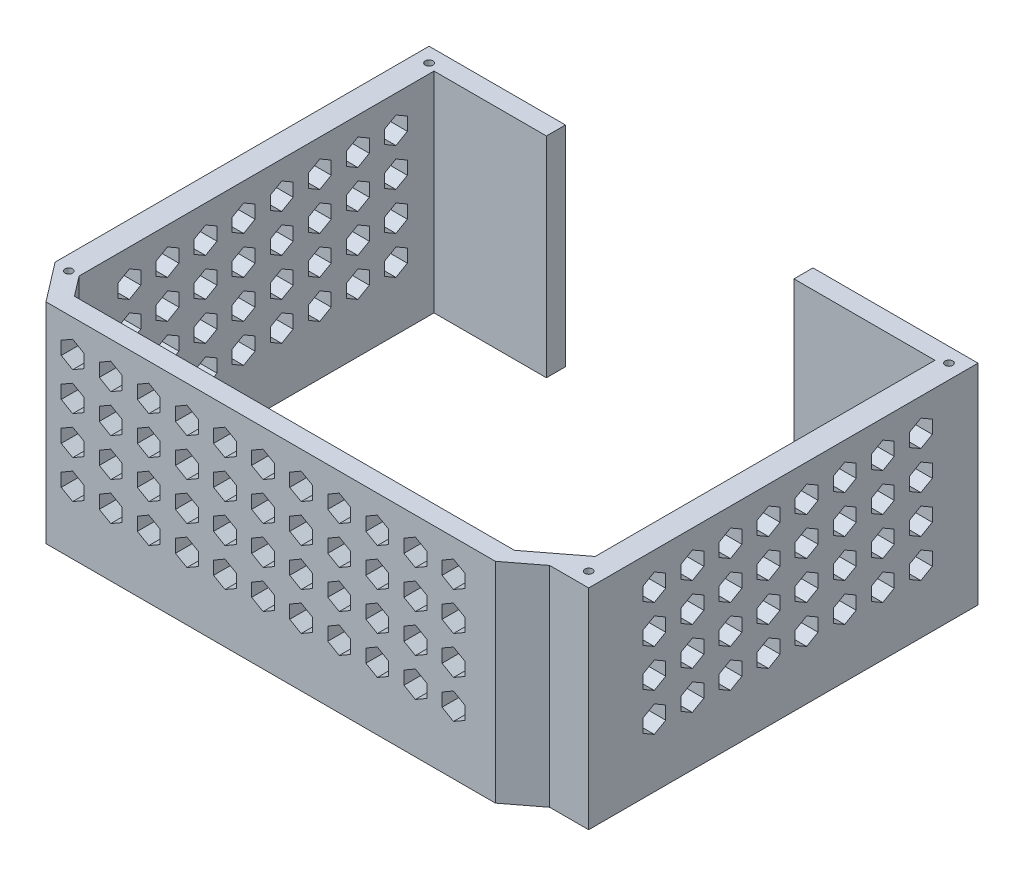
SolidWorks part; units mm, degrees
ref_plane "Front Plane" through (0, 0, 0) normal (0, 0, 1) x (1, 0, 0)
ref_plane "Top Plane" through (0, 0, 0) normal (0, 1, 0) x (1, 0, 0)
ref_plane "Right Plane" through (0, 0, 0) normal (1, 0, 0) x (0, 0, -1)
sketch "Sketch1" plane through (0, 0, 0) normal (0, 1, 0) x (1, 0, 0)
  line L0 (68.26, 0) -> (68.26, 47.305) construction
  line L1 (68.26, 47.305) -> (0, 47.305) construction
  line L2 (-3.815, 98.425) -> (-3.815, 0.2182)
  line L4 (-3.815, 0.2182) -> (4.0178, -10)
  line L5 (4.0178, -10) -> (122.03, -10)
  line L6 (122.03, -10) -> (130.0986, -3.815)
  line L7 (130.0986, -3.815) -> (140.33, -3.815)
  line L8 (140.33, -3.815) -> (140.33, 98.425)
  line L9 (140.33, 98.425) -> (97, 98.425)
  line L10 (97, 98.425) -> (97, 93.425)
  line L11 (97, 93.425) -> (134.03, 93.425)
  line L12 (134.03, 93.425) -> (134.03, 4.1986)
  line L13 (134.03, 4.1986) -> (122.03, -5)
  line L14 (122.03, -5) -> (6.485, -5)
  line L15 (6.485, -5) -> (2.485, 0.2182)
  line L16 (2.485, 0.2182) -> (2.485, 93.425)
  line L17 (2.485, 93.425) -> (32, 93.425)
  line L18 (32, 93.425) -> (32, 98.425)
  line L19 (32, 98.425) -> (-3.815, 98.425)
  circle A0 centre (0, 0) radius 1
  circle A1 centre (136.52, 0) radius 1
  circle A2 centre (136.52, 94.61) radius 1
  circle A3 centre (0, 94.61) radius 1
  dimension "D1" = 2
  dimension "D2" = 136.52
  dimension "D3" = 94.61
  dimension "D4" = 144.145
  dimension "D5" = 3.815
  dimension "D6" = 6.3
  dimension "D7" = 3.815
  dimension "D8" = 5
  dimension "D9" = 5
  dimension "D10" = 5
  dimension "D11" = 4
  dimension "D12" = 65
  dimension "D13" = 32
  dimension "D14" = 5
  dimension "D15" = 6.3
  dimension "D16" = 12
  dimension "D17" = 3.815
extrude "Boss-Extrude1" add sketch "Sketch1" along normal blind 55
sketch "Sketch2" plane through (0, 0, 10) normal (0, 0, 1) x (1, 0, 0)
  line L0 (4.0178, 55) -> (4.0178, 0) construction
  line L1 (11.0178, 43.0718) -> (14.0178, 44.8038)
  line L2 (14.0178, 44.8038) -> (14.0178, 48.2679)
  line L3 (14.0178, 48.2679) -> (11.0178, 50)
  line L4 (11.0178, 50) -> (8.0178, 48.2679)
  line L5 (8.0178, 48.2679) -> (8.0178, 44.8038)
  line L6 (8.0178, 44.8038) -> (11.0178, 43.0718)
  line L7 (4.0178, 55) -> (122.03, 55) construction
  line L8 (21.0178, 43.0718) -> (24.0178, 44.8038)
  line L9 (24.0178, 44.8038) -> (24.0178, 48.2679)
  line L10 (24.0178, 48.2679) -> (21.0178, 50)
  line L11 (21.0178, 50) -> (18.0178, 48.2679)
  line L12 (18.0178, 48.2679) -> (18.0178, 44.8038)
  line L13 (18.0178, 44.8038) -> (21.0178, 43.0718)
  line L14 (31.0178, 43.0718) -> (34.0178, 44.8038)
  line L15 (34.0178, 44.8038) -> (34.0178, 48.2679)
  line L16 (34.0178, 48.2679) -> (31.0178, 50)
  line L17 (31.0178, 50) -> (28.0178, 48.2679)
  line L18 (28.0178, 48.2679) -> (28.0178, 44.8038)
  line L19 (28.0178, 44.8038) -> (31.0178, 43.0718)
  line L20 (41.0178, 43.0718) -> (44.0178, 44.8038)
  line L21 (44.0178, 44.8038) -> (44.0178, 48.2679)
  line L22 (44.0178, 48.2679) -> (41.0178, 50)
  line L23 (41.0178, 50) -> (38.0178, 48.2679)
  line L24 (38.0178, 48.2679) -> (38.0178, 44.8038)
  line L25 (38.0178, 44.8038) -> (41.0178, 43.0718)
  line L26 (51.0178, 43.0718) -> (54.0178, 44.8038)
  line L27 (54.0178, 44.8038) -> (54.0178, 48.2679)
  line L28 (54.0178, 48.2679) -> (51.0178, 50)
  line L29 (51.0178, 50) -> (48.0178, 48.2679)
  line L30 (48.0178, 48.2679) -> (48.0178, 44.8038)
  line L31 (48.0178, 44.8038) -> (51.0178, 43.0718)
  line L32 (61.0178, 43.0718) -> (64.0178, 44.8038)
  line L33 (64.0178, 44.8038) -> (64.0178, 48.2679)
  line L34 (64.0178, 48.2679) -> (61.0178, 50)
  line L35 (61.0178, 50) -> (58.0178, 48.2679)
  line L36 (58.0178, 48.2679) -> (58.0178, 44.8038)
  line L37 (58.0178, 44.8038) -> (61.0178, 43.0718)
  line L38 (71.0178, 43.0718) -> (74.0178, 44.8038)
  line L39 (74.0178, 44.8038) -> (74.0178, 48.2679)
  line L40 (74.0178, 48.2679) -> (71.0178, 50)
  line L41 (71.0178, 50) -> (68.0178, 48.2679)
  line L42 (68.0178, 48.2679) -> (68.0178, 44.8038)
  line L43 (68.0178, 44.8038) -> (71.0178, 43.0718)
  line L44 (81.0178, 43.0718) -> (84.0178, 44.8038)
  line L45 (84.0178, 44.8038) -> (84.0178, 48.2679)
  line L46 (84.0178, 48.2679) -> (81.0178, 50)
  line L47 (81.0178, 50) -> (78.0178, 48.2679)
  line L48 (78.0178, 48.2679) -> (78.0178, 44.8038)
  line L49 (78.0178, 44.8038) -> (81.0178, 43.0718)
  line L50 (91.0178, 43.0718) -> (94.0178, 44.8038)
  line L51 (94.0178, 44.8038) -> (94.0178, 48.2679)
  line L52 (94.0178, 48.2679) -> (91.0178, 50)
  line L53 (91.0178, 50) -> (88.0178, 48.2679)
  line L54 (88.0178, 48.2679) -> (88.0178, 44.8038)
  line L55 (88.0178, 44.8038) -> (91.0178, 43.0718)
  line L56 (101.0178, 43.0718) -> (104.0178, 44.8038)
  line L57 (104.0178, 44.8038) -> (104.0178, 48.2679)
  line L58 (104.0178, 48.2679) -> (101.0178, 50)
  line L59 (101.0178, 50) -> (98.0178, 48.2679)
  line L60 (98.0178, 48.2679) -> (98.0178, 44.8038)
  line L61 (98.0178, 44.8038) -> (101.0178, 43.0718)
  line L62 (111.0178, 43.0718) -> (114.0178, 44.8038)
  line L63 (114.0178, 44.8038) -> (114.0178, 48.2679)
  line L64 (114.0178, 48.2679) -> (111.0178, 50)
  line L65 (111.0178, 50) -> (108.0178, 48.2679)
  line L66 (108.0178, 48.2679) -> (108.0178, 44.8038)
  line L67 (108.0178, 44.8038) -> (111.0178, 43.0718)
  line L68 (21.0178, 33.0718) -> (24.0178, 34.8038)
  line L69 (24.0178, 34.8038) -> (24.0178, 38.2679)
  line L70 (24.0178, 38.2679) -> (21.0178, 40)
  line L71 (21.0178, 40) -> (18.0178, 38.2679)
  line L72 (18.0178, 38.2679) -> (18.0178, 34.8038)
  line L73 (18.0178, 34.8038) -> (21.0178, 33.0718)
  line L74 (31.0178, 33.0718) -> (34.0178, 34.8038)
  line L75 (34.0178, 34.8038) -> (34.0178, 38.2679)
  line L76 (34.0178, 38.2679) -> (31.0178, 40)
  line L77 (31.0178, 40) -> (28.0178, 38.2679)
  line L78 (28.0178, 38.2679) -> (28.0178, 34.8038)
  line L79 (28.0178, 34.8038) -> (31.0178, 33.0718)
  line L80 (41.0178, 33.0718) -> (44.0178, 34.8038)
  line L81 (44.0178, 34.8038) -> (44.0178, 38.2679)
  line L82 (44.0178, 38.2679) -> (41.0178, 40)
  line L83 (41.0178, 40) -> (38.0178, 38.2679)
  line L84 (38.0178, 38.2679) -> (38.0178, 34.8038)
  line L85 (38.0178, 34.8038) -> (41.0178, 33.0718)
  line L86 (51.0178, 33.0718) -> (54.0178, 34.8038)
  line L87 (54.0178, 34.8038) -> (54.0178, 38.2679)
  line L88 (54.0178, 38.2679) -> (51.0178, 40)
  line L89 (51.0178, 40) -> (48.0178, 38.2679)
  line L90 (48.0178, 38.2679) -> (48.0178, 34.8038)
  line L91 (48.0178, 34.8038) -> (51.0178, 33.0718)
  line L92 (61.0178, 33.0718) -> (64.0178, 34.8038)
  line L93 (64.0178, 34.8038) -> (64.0178, 38.2679)
  line L94 (64.0178, 38.2679) -> (61.0178, 40)
  line L95 (61.0178, 40) -> (58.0178, 38.2679)
  line L96 (58.0178, 38.2679) -> (58.0178, 34.8038)
  line L97 (58.0178, 34.8038) -> (61.0178, 33.0718)
  line L98 (71.0178, 33.0718) -> (74.0178, 34.8038)
  line L99 (74.0178, 34.8038) -> (74.0178, 38.2679)
  line L100 (74.0178, 38.2679) -> (71.0178, 40)
  line L101 (71.0178, 40) -> (68.0178, 38.2679)
  line L102 (68.0178, 38.2679) -> (68.0178, 34.8038)
  line L103 (68.0178, 34.8038) -> (71.0178, 33.0718)
  line L104 (81.0178, 33.0718) -> (84.0178, 34.8038)
  line L105 (84.0178, 34.8038) -> (84.0178, 38.2679)
  line L106 (84.0178, 38.2679) -> (81.0178, 40)
  line L107 (81.0178, 40) -> (78.0178, 38.2679)
  line L108 (78.0178, 38.2679) -> (78.0178, 34.8038)
  line L109 (78.0178, 34.8038) -> (81.0178, 33.0718)
  line L110 (91.0178, 33.0718) -> (94.0178, 34.8038)
  line L111 (94.0178, 34.8038) -> (94.0178, 38.2679)
  line L112 (94.0178, 38.2679) -> (91.0178, 40)
  line L113 (91.0178, 40) -> (88.0178, 38.2679)
  line L114 (88.0178, 38.2679) -> (88.0178, 34.8038)
  line L115 (88.0178, 34.8038) -> (91.0178, 33.0718)
  line L116 (101.0178, 33.0718) -> (104.0178, 34.8038)
  line L117 (104.0178, 34.8038) -> (104.0178, 38.2679)
  line L118 (104.0178, 38.2679) -> (101.0178, 40)
  line L119 (101.0178, 40) -> (98.0178, 38.2679)
  line L120 (98.0178, 38.2679) -> (98.0178, 34.8038)
  line L121 (98.0178, 34.8038) -> (101.0178, 33.0718)
  line L122 (111.0178, 33.0718) -> (114.0178, 34.8038)
  line L123 (114.0178, 34.8038) -> (114.0178, 38.2679)
  line L124 (114.0178, 38.2679) -> (111.0178, 40)
  line L125 (111.0178, 40) -> (108.0178, 38.2679)
  line L126 (108.0178, 38.2679) -> (108.0178, 34.8038)
  line L127 (108.0178, 34.8038) -> (111.0178, 33.0718)
  line L128 (21.0178, 23.0718) -> (24.0178, 24.8038)
  line L129 (24.0178, 24.8038) -> (24.0178, 28.2679)
  line L130 (24.0178, 28.2679) -> (21.0178, 30)
  line L131 (21.0178, 30) -> (18.0178, 28.2679)
  line L132 (18.0178, 28.2679) -> (18.0178, 24.8038)
  line L133 (18.0178, 24.8038) -> (21.0178, 23.0718)
  line L134 (31.0178, 23.0718) -> (34.0178, 24.8038)
  line L135 (34.0178, 24.8038) -> (34.0178, 28.2679)
  line L136 (34.0178, 28.2679) -> (31.0178, 30)
  line L137 (31.0178, 30) -> (28.0178, 28.2679)
  line L138 (28.0178, 28.2679) -> (28.0178, 24.8038)
  line L139 (28.0178, 24.8038) -> (31.0178, 23.0718)
  line L140 (41.0178, 23.0718) -> (44.0178, 24.8038)
  line L141 (44.0178, 24.8038) -> (44.0178, 28.2679)
  line L142 (44.0178, 28.2679) -> (41.0178, 30)
  line L143 (41.0178, 30) -> (38.0178, 28.2679)
  line L144 (38.0178, 28.2679) -> (38.0178, 24.8038)
  line L145 (38.0178, 24.8038) -> (41.0178, 23.0718)
  line L146 (51.0178, 23.0718) -> (54.0178, 24.8038)
  line L147 (54.0178, 24.8038) -> (54.0178, 28.2679)
  line L148 (54.0178, 28.2679) -> (51.0178, 30)
  line L149 (51.0178, 30) -> (48.0178, 28.2679)
  line L150 (48.0178, 28.2679) -> (48.0178, 24.8038)
  line L151 (48.0178, 24.8038) -> (51.0178, 23.0718)
  line L152 (61.0178, 23.0718) -> (64.0178, 24.8038)
  line L153 (64.0178, 24.8038) -> (64.0178, 28.2679)
  line L154 (64.0178, 28.2679) -> (61.0178, 30)
  line L155 (61.0178, 30) -> (58.0178, 28.2679)
  line L156 (58.0178, 28.2679) -> (58.0178, 24.8038)
  line L157 (58.0178, 24.8038) -> (61.0178, 23.0718)
  line L158 (71.0178, 23.0718) -> (74.0178, 24.8038)
  line L159 (74.0178, 24.8038) -> (74.0178, 28.2679)
  line L160 (74.0178, 28.2679) -> (71.0178, 30)
  line L161 (71.0178, 30) -> (68.0178, 28.2679)
  line L162 (68.0178, 28.2679) -> (68.0178, 24.8038)
  line L163 (68.0178, 24.8038) -> (71.0178, 23.0718)
  line L164 (81.0178, 23.0718) -> (84.0178, 24.8038)
  line L165 (84.0178, 24.8038) -> (84.0178, 28.2679)
  line L166 (84.0178, 28.2679) -> (81.0178, 30)
  line L167 (81.0178, 30) -> (78.0178, 28.2679)
  line L168 (78.0178, 28.2679) -> (78.0178, 24.8038)
  line L169 (78.0178, 24.8038) -> (81.0178, 23.0718)
  line L170 (91.0178, 23.0718) -> (94.0178, 24.8038)
  line L171 (94.0178, 24.8038) -> (94.0178, 28.2679)
  line L172 (94.0178, 28.2679) -> (91.0178, 30)
  line L173 (91.0178, 30) -> (88.0178, 28.2679)
  line L174 (88.0178, 28.2679) -> (88.0178, 24.8038)
  line L175 (88.0178, 24.8038) -> (91.0178, 23.0718)
  line L176 (101.0178, 23.0718) -> (104.0178, 24.8038)
  line L177 (104.0178, 24.8038) -> (104.0178, 28.2679)
  line L178 (104.0178, 28.2679) -> (101.0178, 30)
  line L179 (101.0178, 30) -> (98.0178, 28.2679)
  line L180 (98.0178, 28.2679) -> (98.0178, 24.8038)
  line L181 (98.0178, 24.8038) -> (101.0178, 23.0718)
  line L182 (111.0178, 23.0718) -> (114.0178, 24.8038)
  line L183 (114.0178, 24.8038) -> (114.0178, 28.2679)
  line L184 (114.0178, 28.2679) -> (111.0178, 30)
  line L185 (111.0178, 30) -> (108.0178, 28.2679)
  line L186 (108.0178, 28.2679) -> (108.0178, 24.8038)
  line L187 (108.0178, 24.8038) -> (111.0178, 23.0718)
  line L188 (21.0178, 13.0718) -> (24.0178, 14.8038)
  line L189 (24.0178, 14.8038) -> (24.0178, 18.2679)
  line L190 (24.0178, 18.2679) -> (21.0178, 20)
  line L191 (21.0178, 20) -> (18.0178, 18.2679)
  line L192 (18.0178, 18.2679) -> (18.0178, 14.8038)
  line L193 (18.0178, 14.8038) -> (21.0178, 13.0718)
  line L194 (31.0178, 13.0718) -> (34.0178, 14.8038)
  line L195 (34.0178, 14.8038) -> (34.0178, 18.2679)
  line L196 (34.0178, 18.2679) -> (31.0178, 20)
  line L197 (31.0178, 20) -> (28.0178, 18.2679)
  line L198 (28.0178, 18.2679) -> (28.0178, 14.8038)
  line L199 (28.0178, 14.8038) -> (31.0178, 13.0718)
  line L200 (41.0178, 13.0718) -> (44.0178, 14.8038)
  line L201 (44.0178, 14.8038) -> (44.0178, 18.2679)
  line L202 (44.0178, 18.2679) -> (41.0178, 20)
  line L203 (41.0178, 20) -> (38.0178, 18.2679)
  line L204 (38.0178, 18.2679) -> (38.0178, 14.8038)
  line L205 (38.0178, 14.8038) -> (41.0178, 13.0718)
  line L206 (51.0178, 13.0718) -> (54.0178, 14.8038)
  line L207 (54.0178, 14.8038) -> (54.0178, 18.2679)
  line L208 (54.0178, 18.2679) -> (51.0178, 20)
  line L209 (51.0178, 20) -> (48.0178, 18.2679)
  line L210 (48.0178, 18.2679) -> (48.0178, 14.8038)
  line L211 (48.0178, 14.8038) -> (51.0178, 13.0718)
  line L212 (61.0178, 13.0718) -> (64.0178, 14.8038)
  line L213 (64.0178, 14.8038) -> (64.0178, 18.2679)
  line L214 (64.0178, 18.2679) -> (61.0178, 20)
  line L215 (61.0178, 20) -> (58.0178, 18.2679)
  line L216 (58.0178, 18.2679) -> (58.0178, 14.8038)
  line L217 (58.0178, 14.8038) -> (61.0178, 13.0718)
  line L218 (71.0178, 13.0718) -> (74.0178, 14.8038)
  line L219 (74.0178, 14.8038) -> (74.0178, 18.2679)
  line L220 (74.0178, 18.2679) -> (71.0178, 20)
  line L221 (71.0178, 20) -> (68.0178, 18.2679)
  line L222 (68.0178, 18.2679) -> (68.0178, 14.8038)
  line L223 (68.0178, 14.8038) -> (71.0178, 13.0718)
  line L224 (81.0178, 13.0718) -> (84.0178, 14.8038)
  line L225 (84.0178, 14.8038) -> (84.0178, 18.2679)
  line L226 (84.0178, 18.2679) -> (81.0178, 20)
  line L227 (81.0178, 20) -> (78.0178, 18.2679)
  line L228 (78.0178, 18.2679) -> (78.0178, 14.8038)
  line L229 (78.0178, 14.8038) -> (81.0178, 13.0718)
  line L230 (91.0178, 13.0718) -> (94.0178, 14.8038)
  line L231 (94.0178, 14.8038) -> (94.0178, 18.2679)
  line L232 (94.0178, 18.2679) -> (91.0178, 20)
  line L233 (91.0178, 20) -> (88.0178, 18.2679)
  line L234 (88.0178, 18.2679) -> (88.0178, 14.8038)
  line L235 (88.0178, 14.8038) -> (91.0178, 13.0718)
  line L236 (101.0178, 13.0718) -> (104.0178, 14.8038)
  line L237 (104.0178, 14.8038) -> (104.0178, 18.2679)
  line L238 (104.0178, 18.2679) -> (101.0178, 20)
  line L239 (101.0178, 20) -> (98.0178, 18.2679)
  line L240 (98.0178, 18.2679) -> (98.0178, 14.8038)
  line L241 (98.0178, 14.8038) -> (101.0178, 13.0718)
  line L242 (111.0178, 13.0718) -> (114.0178, 14.8038)
  line L243 (114.0178, 14.8038) -> (114.0178, 18.2679)
  line L244 (114.0178, 18.2679) -> (111.0178, 20)
  line L245 (111.0178, 20) -> (108.0178, 18.2679)
  line L246 (108.0178, 18.2679) -> (108.0178, 14.8038)
  line L247 (108.0178, 14.8038) -> (111.0178, 13.0718)
  line L248 (11.0178, 33.0718) -> (14.0178, 34.8038)
  line L249 (14.0178, 34.8038) -> (14.0178, 38.2679)
  line L250 (14.0178, 38.2679) -> (11.0178, 40)
  line L251 (11.0178, 40) -> (8.0178, 38.2679)
  line L252 (8.0178, 38.2679) -> (8.0178, 34.8038)
  line L253 (8.0178, 34.8038) -> (11.0178, 33.0718)
  line L254 (11.0178, 23.0718) -> (14.0178, 24.8038)
  line L255 (14.0178, 24.8038) -> (14.0178, 28.2679)
  line L256 (14.0178, 28.2679) -> (11.0178, 30)
  line L257 (11.0178, 30) -> (8.0178, 28.2679)
  line L258 (8.0178, 28.2679) -> (8.0178, 24.8038)
  line L259 (8.0178, 24.8038) -> (11.0178, 23.0718)
  line L260 (11.0178, 13.0718) -> (14.0178, 14.8038)
  line L261 (14.0178, 14.8038) -> (14.0178, 18.2679)
  line L262 (14.0178, 18.2679) -> (11.0178, 20)
  line L263 (11.0178, 20) -> (8.0178, 18.2679)
  line L264 (8.0178, 18.2679) -> (8.0178, 14.8038)
  line L265 (8.0178, 14.8038) -> (11.0178, 13.0718)
  circle A0 centre (11.0178, 46.5359) radius 3 construction
  dimension "D1" = 6
  dimension "D2" = 4
  dimension "D3" = 5
  dimension "D6" = 4
  dimension "D7" = 3.0718
  dimension "D4" = 11
  dimension "D5" = 4
extrude "Cut-Extrude1" cut sketch "Sketch2" against normal up to surface (5 mm away) up to face at (64.2575, 27.5, 5)
sketch "Sketch3" plane through (-3.815, 0, 0) normal (-1, 0, 0) x (0, 0, 1)
  line L0 (-98.425, 55) -> (-0.2182, 55) construction
  line L1 (-83.425, 43.0718) -> (-80.425, 44.8038)
  line L2 (-80.425, 44.8038) -> (-80.425, 48.2679)
  line L3 (-80.425, 48.2679) -> (-83.425, 50)
  line L4 (-83.425, 50) -> (-86.425, 48.2679)
  line L5 (-86.425, 48.2679) -> (-86.425, 44.8038)
  line L6 (-86.425, 44.8038) -> (-83.425, 43.0718)
  line L7 (-98.425, 55) -> (-98.425, 0) construction
  line L8 (-73.425, 43.0718) -> (-70.425, 44.8038)
  line L9 (-70.425, 44.8038) -> (-70.425, 48.2679)
  line L10 (-70.425, 48.2679) -> (-73.425, 50)
  line L11 (-73.425, 50) -> (-76.425, 48.2679)
  line L12 (-76.425, 48.2679) -> (-76.425, 44.8038)
  line L13 (-76.425, 44.8038) -> (-73.425, 43.0718)
  line L14 (-63.425, 43.0718) -> (-60.425, 44.8038)
  line L15 (-60.425, 44.8038) -> (-60.425, 48.2679)
  line L16 (-60.425, 48.2679) -> (-63.425, 50)
  line L17 (-63.425, 50) -> (-66.425, 48.2679)
  line L18 (-66.425, 48.2679) -> (-66.425, 44.8038)
  line L19 (-66.425, 44.8038) -> (-63.425, 43.0718)
  line L20 (-53.425, 43.0718) -> (-50.425, 44.8038)
  line L21 (-50.425, 44.8038) -> (-50.425, 48.2679)
  line L22 (-50.425, 48.2679) -> (-53.425, 50)
  line L23 (-53.425, 50) -> (-56.425, 48.2679)
  line L24 (-56.425, 48.2679) -> (-56.425, 44.8038)
  line L25 (-56.425, 44.8038) -> (-53.425, 43.0718)
  line L26 (-43.425, 43.0718) -> (-40.425, 44.8038)
  line L27 (-40.425, 44.8038) -> (-40.425, 48.2679)
  line L28 (-40.425, 48.2679) -> (-43.425, 50)
  line L29 (-43.425, 50) -> (-46.425, 48.2679)
  line L30 (-46.425, 48.2679) -> (-46.425, 44.8038)
  line L31 (-46.425, 44.8038) -> (-43.425, 43.0718)
  line L32 (-33.425, 43.0718) -> (-30.425, 44.8038)
  line L33 (-30.425, 44.8038) -> (-30.425, 48.2679)
  line L34 (-30.425, 48.2679) -> (-33.425, 50)
  line L35 (-33.425, 50) -> (-36.425, 48.2679)
  line L36 (-36.425, 48.2679) -> (-36.425, 44.8038)
  line L37 (-36.425, 44.8038) -> (-33.425, 43.0718)
  line L38 (-23.425, 43.0718) -> (-20.425, 44.8038)
  line L39 (-20.425, 44.8038) -> (-20.425, 48.2679)
  line L40 (-20.425, 48.2679) -> (-23.425, 50)
  line L41 (-23.425, 50) -> (-26.425, 48.2679)
  line L42 (-26.425, 48.2679) -> (-26.425, 44.8038)
  line L43 (-26.425, 44.8038) -> (-23.425, 43.0718)
  line L44 (-13.425, 43.0718) -> (-10.425, 44.8038)
  line L45 (-10.425, 44.8038) -> (-10.425, 48.2679)
  line L46 (-10.425, 48.2679) -> (-13.425, 50)
  line L47 (-13.425, 50) -> (-16.425, 48.2679)
  line L48 (-16.425, 48.2679) -> (-16.425, 44.8038)
  line L49 (-16.425, 44.8038) -> (-13.425, 43.0718)
  line L50 (-73.425, 33.0718) -> (-70.425, 34.8038)
  line L51 (-70.425, 34.8038) -> (-70.425, 38.2679)
  line L52 (-70.425, 38.2679) -> (-73.425, 40)
  line L53 (-73.425, 40) -> (-76.425, 38.2679)
  line L54 (-76.425, 38.2679) -> (-76.425, 34.8038)
  line L55 (-76.425, 34.8038) -> (-73.425, 33.0718)
  line L56 (-63.425, 33.0718) -> (-60.425, 34.8038)
  line L57 (-60.425, 34.8038) -> (-60.425, 38.2679)
  line L58 (-60.425, 38.2679) -> (-63.425, 40)
  line L59 (-63.425, 40) -> (-66.425, 38.2679)
  line L60 (-66.425, 38.2679) -> (-66.425, 34.8038)
  line L61 (-66.425, 34.8038) -> (-63.425, 33.0718)
  line L62 (-53.425, 33.0718) -> (-50.425, 34.8038)
  line L63 (-50.425, 34.8038) -> (-50.425, 38.2679)
  line L64 (-50.425, 38.2679) -> (-53.425, 40)
  line L65 (-53.425, 40) -> (-56.425, 38.2679)
  line L66 (-56.425, 38.2679) -> (-56.425, 34.8038)
  line L67 (-56.425, 34.8038) -> (-53.425, 33.0718)
  line L68 (-43.425, 33.0718) -> (-40.425, 34.8038)
  line L69 (-40.425, 34.8038) -> (-40.425, 38.2679)
  line L70 (-40.425, 38.2679) -> (-43.425, 40)
  line L71 (-43.425, 40) -> (-46.425, 38.2679)
  line L72 (-46.425, 38.2679) -> (-46.425, 34.8038)
  line L73 (-46.425, 34.8038) -> (-43.425, 33.0718)
  line L74 (-33.425, 33.0718) -> (-30.425, 34.8038)
  line L75 (-30.425, 34.8038) -> (-30.425, 38.2679)
  line L76 (-30.425, 38.2679) -> (-33.425, 40)
  line L77 (-33.425, 40) -> (-36.425, 38.2679)
  line L78 (-36.425, 38.2679) -> (-36.425, 34.8038)
  line L79 (-36.425, 34.8038) -> (-33.425, 33.0718)
  line L80 (-23.425, 33.0718) -> (-20.425, 34.8038)
  line L81 (-20.425, 34.8038) -> (-20.425, 38.2679)
  line L82 (-20.425, 38.2679) -> (-23.425, 40)
  line L83 (-23.425, 40) -> (-26.425, 38.2679)
  line L84 (-26.425, 38.2679) -> (-26.425, 34.8038)
  line L85 (-26.425, 34.8038) -> (-23.425, 33.0718)
  line L86 (-13.425, 33.0718) -> (-10.425, 34.8038)
  line L87 (-10.425, 34.8038) -> (-10.425, 38.2679)
  line L88 (-10.425, 38.2679) -> (-13.425, 40)
  line L89 (-13.425, 40) -> (-16.425, 38.2679)
  line L90 (-16.425, 38.2679) -> (-16.425, 34.8038)
  line L91 (-16.425, 34.8038) -> (-13.425, 33.0718)
  line L92 (-73.425, 23.0718) -> (-70.425, 24.8038)
  line L93 (-70.425, 24.8038) -> (-70.425, 28.2679)
  line L94 (-70.425, 28.2679) -> (-73.425, 30)
  line L95 (-73.425, 30) -> (-76.425, 28.2679)
  line L96 (-76.425, 28.2679) -> (-76.425, 24.8038)
  line L97 (-76.425, 24.8038) -> (-73.425, 23.0718)
  line L98 (-63.425, 23.0718) -> (-60.425, 24.8038)
  line L99 (-60.425, 24.8038) -> (-60.425, 28.2679)
  line L100 (-60.425, 28.2679) -> (-63.425, 30)
  line L101 (-63.425, 30) -> (-66.425, 28.2679)
  line L102 (-66.425, 28.2679) -> (-66.425, 24.8038)
  line L103 (-66.425, 24.8038) -> (-63.425, 23.0718)
  line L104 (-53.425, 23.0718) -> (-50.425, 24.8038)
  line L105 (-50.425, 24.8038) -> (-50.425, 28.2679)
  line L106 (-50.425, 28.2679) -> (-53.425, 30)
  line L107 (-53.425, 30) -> (-56.425, 28.2679)
  line L108 (-56.425, 28.2679) -> (-56.425, 24.8038)
  line L109 (-56.425, 24.8038) -> (-53.425, 23.0718)
  line L110 (-43.425, 23.0718) -> (-40.425, 24.8038)
  line L111 (-40.425, 24.8038) -> (-40.425, 28.2679)
  line L112 (-40.425, 28.2679) -> (-43.425, 30)
  line L113 (-43.425, 30) -> (-46.425, 28.2679)
  line L114 (-46.425, 28.2679) -> (-46.425, 24.8038)
  line L115 (-46.425, 24.8038) -> (-43.425, 23.0718)
  line L116 (-33.425, 23.0718) -> (-30.425, 24.8038)
  line L117 (-30.425, 24.8038) -> (-30.425, 28.2679)
  line L118 (-30.425, 28.2679) -> (-33.425, 30)
  line L119 (-33.425, 30) -> (-36.425, 28.2679)
  line L120 (-36.425, 28.2679) -> (-36.425, 24.8038)
  line L121 (-36.425, 24.8038) -> (-33.425, 23.0718)
  line L122 (-23.425, 23.0718) -> (-20.425, 24.8038)
  line L123 (-20.425, 24.8038) -> (-20.425, 28.2679)
  line L124 (-20.425, 28.2679) -> (-23.425, 30)
  line L125 (-23.425, 30) -> (-26.425, 28.2679)
  line L126 (-26.425, 28.2679) -> (-26.425, 24.8038)
  line L127 (-26.425, 24.8038) -> (-23.425, 23.0718)
  line L128 (-13.425, 23.0718) -> (-10.425, 24.8038)
  line L129 (-10.425, 24.8038) -> (-10.425, 28.2679)
  line L130 (-10.425, 28.2679) -> (-13.425, 30)
  line L131 (-13.425, 30) -> (-16.425, 28.2679)
  line L132 (-16.425, 28.2679) -> (-16.425, 24.8038)
  line L133 (-16.425, 24.8038) -> (-13.425, 23.0718)
  line L134 (-73.425, 13.0718) -> (-70.425, 14.8038)
  line L135 (-70.425, 14.8038) -> (-70.425, 18.2679)
  line L136 (-70.425, 18.2679) -> (-73.425, 20)
  line L137 (-73.425, 20) -> (-76.425, 18.2679)
  line L138 (-76.425, 18.2679) -> (-76.425, 14.8038)
  line L139 (-76.425, 14.8038) -> (-73.425, 13.0718)
  line L140 (-63.425, 13.0718) -> (-60.425, 14.8038)
  line L141 (-60.425, 14.8038) -> (-60.425, 18.2679)
  line L142 (-60.425, 18.2679) -> (-63.425, 20)
  line L143 (-63.425, 20) -> (-66.425, 18.2679)
  line L144 (-66.425, 18.2679) -> (-66.425, 14.8038)
  line L145 (-66.425, 14.8038) -> (-63.425, 13.0718)
  line L146 (-53.425, 13.0718) -> (-50.425, 14.8038)
  line L147 (-50.425, 14.8038) -> (-50.425, 18.2679)
  line L148 (-50.425, 18.2679) -> (-53.425, 20)
  line L149 (-53.425, 20) -> (-56.425, 18.2679)
  line L150 (-56.425, 18.2679) -> (-56.425, 14.8038)
  line L151 (-56.425, 14.8038) -> (-53.425, 13.0718)
  line L152 (-43.425, 13.0718) -> (-40.425, 14.8038)
  line L153 (-40.425, 14.8038) -> (-40.425, 18.2679)
  line L154 (-40.425, 18.2679) -> (-43.425, 20)
  line L155 (-43.425, 20) -> (-46.425, 18.2679)
  line L156 (-46.425, 18.2679) -> (-46.425, 14.8038)
  line L157 (-46.425, 14.8038) -> (-43.425, 13.0718)
  line L158 (-33.425, 13.0718) -> (-30.425, 14.8038)
  line L159 (-30.425, 14.8038) -> (-30.425, 18.2679)
  line L160 (-30.425, 18.2679) -> (-33.425, 20)
  line L161 (-33.425, 20) -> (-36.425, 18.2679)
  line L162 (-36.425, 18.2679) -> (-36.425, 14.8038)
  line L163 (-36.425, 14.8038) -> (-33.425, 13.0718)
  line L164 (-23.425, 13.0718) -> (-20.425, 14.8038)
  line L165 (-20.425, 14.8038) -> (-20.425, 18.2679)
  line L166 (-20.425, 18.2679) -> (-23.425, 20)
  line L167 (-23.425, 20) -> (-26.425, 18.2679)
  line L168 (-26.425, 18.2679) -> (-26.425, 14.8038)
  line L169 (-26.425, 14.8038) -> (-23.425, 13.0718)
  line L170 (-13.425, 13.0718) -> (-10.425, 14.8038)
  line L171 (-10.425, 14.8038) -> (-10.425, 18.2679)
  line L172 (-10.425, 18.2679) -> (-13.425, 20)
  line L173 (-13.425, 20) -> (-16.425, 18.2679)
  line L174 (-16.425, 18.2679) -> (-16.425, 14.8038)
  line L175 (-16.425, 14.8038) -> (-13.425, 13.0718)
  line L176 (-83.425, 33.0718) -> (-80.425, 34.8038)
  line L177 (-80.425, 34.8038) -> (-80.425, 38.2679)
  line L178 (-80.425, 38.2679) -> (-83.425, 40)
  line L179 (-83.425, 40) -> (-86.425, 38.2679)
  line L180 (-86.425, 38.2679) -> (-86.425, 34.8038)
  line L181 (-86.425, 34.8038) -> (-83.425, 33.0718)
  line L182 (-83.425, 23.0718) -> (-80.425, 24.8038)
  line L183 (-80.425, 24.8038) -> (-80.425, 28.2679)
  line L184 (-80.425, 28.2679) -> (-83.425, 30)
  line L185 (-83.425, 30) -> (-86.425, 28.2679)
  line L186 (-86.425, 28.2679) -> (-86.425, 24.8038)
  line L187 (-86.425, 24.8038) -> (-83.425, 23.0718)
  line L188 (-83.425, 13.0718) -> (-80.425, 14.8038)
  line L189 (-80.425, 14.8038) -> (-80.425, 18.2679)
  line L190 (-80.425, 18.2679) -> (-83.425, 20)
  line L191 (-83.425, 20) -> (-86.425, 18.2679)
  line L192 (-86.425, 18.2679) -> (-86.425, 14.8038)
  line L193 (-86.425, 14.8038) -> (-83.425, 13.0718)
  circle A0 centre (-83.425, 46.5359) radius 3 construction
  dimension "D1" = 6
  dimension "D2" = 5
  dimension "D3" = 12
  dimension "D6" = 4
  dimension "D7" = 3.0718
  dimension "D4" = 8
  dimension "D5" = 4
extrude "Cut-Extrude2" cut sketch "Sketch3" against normal through all
